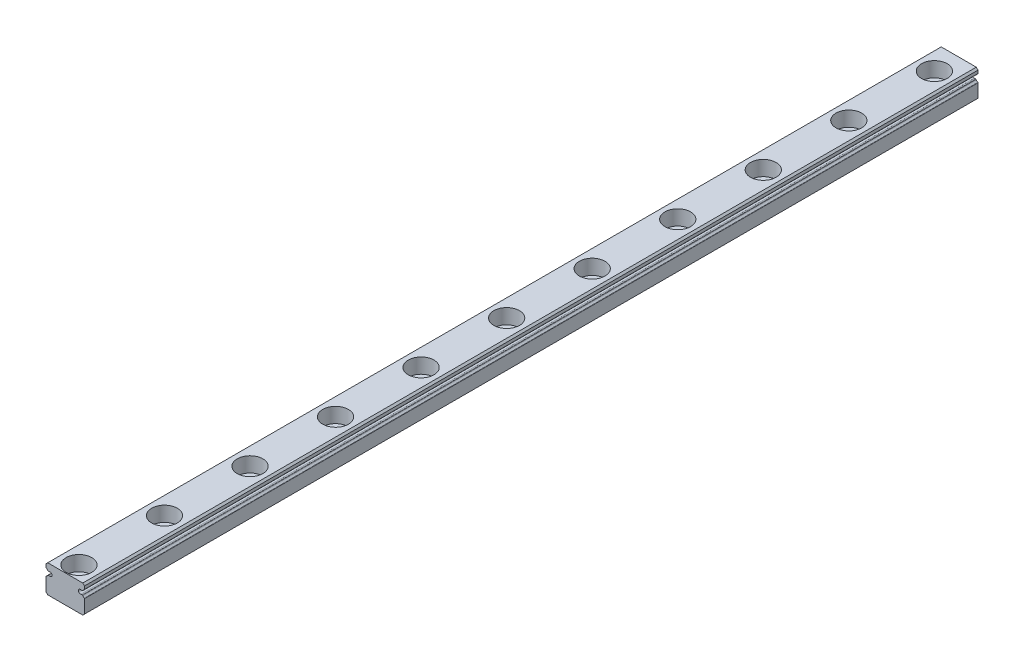
SolidWorks part; units mm, degrees
ref_plane "Front plane" through (0, 0, 0) normal (0, 0, 1) x (1, 0, 0)
ref_plane "Top plane" through (0, 0, 0) normal (0, 1, 0) x (1, 0, 0)
ref_plane "Right Plane" through (0, 0, 0) normal (1, 0, 0) x (0, 0, -1)
sketch "Sketch1" plane through (0, 0, 0) normal (0, 0, 1) x (1, 0, 0)
  line L0 (-4.1, 6.5) -> (-4.5, 6.1)
  line L1 (-4.1, 0) -> (4.1, 0)
  line L2 (-4.5, 0.4) -> (-4.5, 3.508)
  line L3 (-4.1, 6.5) -> (4.1, 6.5)
  line L4 (4.5, 0.4) -> (4.5, 3.508)
  line L5 (-4.5, 0.4) -> (-4.1, 0)
  line L6 (4.5, 5.412) -> (4.5, 6.1)
  line L7 (4.1, 6.5) -> (4.5, 6.1)
  line L8 (3.9535, 4.885) -> (3.6884, 4.885)
  line L10 (3.9535, 4.035) -> (3.6884, 4.035)
  line L12 (4.1, 0) -> (4.5, 0.4)
  line L13 (0, 6.5) -> (0, 0) construction
  line L14 (-3.9535, 4.035) -> (-3.6884, 4.035)
  line L15 (-3.9535, 4.885) -> (-3.6884, 4.885)
  line L16 (-4.5, 5.412) -> (-4.5, 6.1)
  arc A0 (4.065, 3.9718) -> (4.4314, 3.6226) centre (4.88, 4.46) ccw
  arc A1 (3.6507, 4.8906) -> (3.6507, 4.0294) centre (3.52, 4.46) ccw
  arc A2 (4.4314, 5.2974) -> (4.065, 4.9482) centre (4.88, 4.46) ccw
  arc A3 (3.6884, 4.035) -> (3.6507, 4.0294) centre (3.6884, 3.905) ccw
  arc A4 (3.6884, 4.885) -> (3.6507, 4.8906) centre (3.6884, 5.015) cw
  arc A5 (4.4314, 5.2974) -> (4.5, 5.412) centre (4.37, 5.412) ccw
  arc A6 (3.9535, 4.885) -> (4.065, 4.9482) centre (3.9535, 5.015) ccw
  arc A7 (4.4314, 3.6226) -> (4.5, 3.508) centre (4.37, 3.508) cw
  arc A8 (4.065, 3.9718) -> (3.9535, 4.035) centre (3.9535, 3.905) ccw
  arc A9 (-3.6884, 4.035) -> (-3.6507, 4.0294) centre (-3.6884, 3.905) cw
  arc A10 (-3.6884, 4.885) -> (-3.6507, 4.8906) centre (-3.6884, 5.015) ccw
  arc A11 (-4.4314, 3.6226) -> (-4.5, 3.508) centre (-4.37, 3.508) ccw
  arc A12 (-4.065, 3.9718) -> (-4.4314, 3.6226) centre (-4.88, 4.46) cw
  arc A13 (-4.065, 3.9718) -> (-3.9535, 4.035) centre (-3.9535, 3.905) cw
  arc A14 (-3.6507, 4.8906) -> (-3.6507, 4.0294) centre (-3.52, 4.46) cw
  arc A15 (-3.9535, 4.885) -> (-4.065, 4.9482) centre (-3.9535, 5.015) cw
  arc A16 (-4.4314, 5.2974) -> (-4.065, 4.9482) centre (-4.88, 4.46) cw
  arc A17 (-4.4314, 5.2974) -> (-4.5, 5.412) centre (-4.37, 5.412) cw
  point P24 (3.6679, 4.035)
  point P27 (3.6679, 4.885)
  point P30 (4.5, 5.3307)
  point P33 (4.0304, 4.885)
  point P38 (4.0304, 4.035)
  dimension "D4" = 0.95
  dimension "D6" = 0.45
  dimension "D10" = 0.13
  dimension "D2" = 6.5
  dimension "D3" = 0.4
  dimension "D5" = 0.85
  dimension "D7" = 1.36
  dimension "D8" = 2.04
  dimension "D9" = 0.38
  dimension "D11" = 9
extrude "Boss-Extrude1" add sketch "Sketch1" along normal blind 208.9
sketch "Sketch2" plane through (0, 6.5, 0) normal (0, 1, 0) x (1, 0, 0)
  line L0 (0, -205.7) -> (0, -208.9) construction
  line L1 (4.1, -208.9) -> (-4.1, -208.9) construction
  line L2 (0, 0) -> (0, -25.7) construction
  line L3 (4.1, 0) -> (-4.1, 0) construction
  circle A0 centre (0, -205.7) radius 3
  circle A1 centre (0, -185.7) radius 3
  circle A2 centre (0, -165.7) radius 3
  circle A3 centre (0, -145.7) radius 3
  circle A4 centre (0, -125.7) radius 3
  circle A5 centre (0, -105.7) radius 3
  circle A6 centre (0, -85.7) radius 3
  circle A7 centre (0, -65.7) radius 3
  circle A8 centre (0, -45.7) radius 3
  circle A9 centre (0, -25.7) radius 3
  circle A11 centre (0, -5.7) radius 3 [skipped]
  circle A13 centre (0, -5.7) radius 3
  dimension "D3" = 6
  dimension "D2" = 20
  dimension "D4" = 25.7
  dimension "D5" = 20
  dimension "D1" = 11
extrude "Cut-Extrude1" cut sketch "Sketch2" against normal blind 3.5
sketch "Sketch3" plane through (0, 3, 0) normal (0, 1, 0) x (1, 0, 0)
  circle A0 centre (0, -205.7) radius 1.75
  circle A1 centre (0, -185.7) radius 1.75
  circle A2 centre (0, -165.7) radius 1.75
  circle A3 centre (0, -145.7) radius 1.75
  circle A4 centre (0, -125.7) radius 1.75
  circle A5 centre (0, -105.7) radius 1.75
  circle A6 centre (0, -85.7) radius 1.75
  circle A7 centre (0, -65.7) radius 1.75
  circle A8 centre (0, -45.7) radius 1.75
  circle A9 centre (0, -25.7) radius 1.75
  circle A10 centre (0, -5.7) radius 1.75
  circle A11 centre (0, 14.3) radius 1.75
  dimension "D1" = 3.5
  dimension "D3" = 20
  dimension "D2" = 12
extrude "Cut-Extrude2" cut sketch "Sketch3" against normal through all
